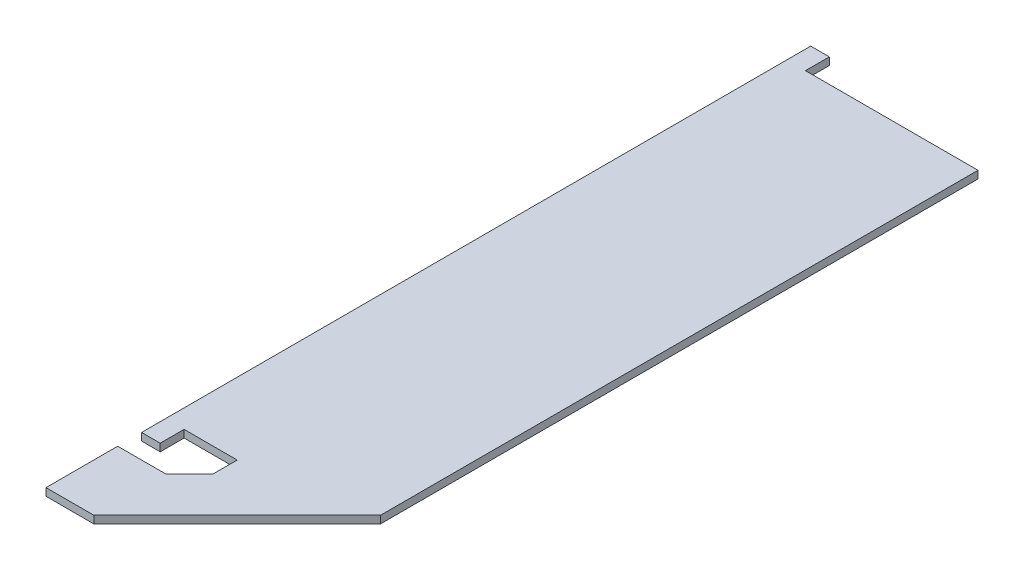
SolidWorks part; units mm, degrees
ref_plane "Front Plane" through (0, 0, 0) normal (0, 0, 1) x (1, 0, 0)
ref_plane "Top Plane" through (0, 0, 0) normal (0, 1, 0) x (1, 0, 0)
ref_plane "Right Plane" through (0, 0, 0) normal (1, 0, 0) x (0, 0, -1)
sketch "Sketch1" plane through (0, 0, 0) normal (0, 1, 0) x (1, 0, 0)
  line L0 (-3.175, -41.275) -> (-3.175, -47.625)
  line L1 (-12.7, -41.275) -> (-3.175, -41.275)
  line L2 (-12.7, -41.275) -> (-12.7, 41.275)
  line L3 (-12.7, 41.275) -> (12.7, 41.275)
  line L4 (12.7, -41.275) -> (12.7, 41.275)
  line L5 (-12.7, -41.275) -> (12.7, 41.275) construction
  line L6 (-12.7, 41.275) -> (12.7, -41.275) construction
  line L7 (-3.175, -47.625) -> (-12.7, -47.625)
  line L8 (-12.7, -47.625) -> (-12.7, -57.15)
  line L9 (-12.7, -57.15) -> (12.7, -57.15)
  line L10 (12.7, -57.15) -> (12.7, -41.275)
  point P0 (0, 0)
  dimension "D1" = 25.4
  dimension "D2" = 82.55
  dimension "D3" = 15.875
  dimension "D4" = 6.35
  dimension "D5" = 15.875
extrude "Boss-Extrude1" add sketch "Sketch1" along normal blind 1.0008
sketch "Sketch2" plane through (0, 0, 41.275) normal (0, 0, 1) x (1, 0, 0)
  line L0 (-12.7, 1.0008) -> (-3.175, 1.0008) construction
  line L1 (-12.7, 0) -> (-10.2279, 0)
  line L2 (-12.7, 0) -> (-12.7, 1.0008)
  line L3 (-12.7, 1.0008) -> (-10.2279, 1.0008)
  line L4 (-10.2279, 0) -> (-10.2279, 1.0008)
  dimension "D1" = 2.667
extrude "Boss-Extrude2" add sketch "Sketch2" along normal blind 3.175
mirror "Mirror1" about plane through (0, 0, 0) normal (0, 0, 1) of "Boss-Extrude2"
chamfer "Chamfer2" distance 19.05 angle 45 1 edges at (12.7, 0.5004, 57.15)
chamfer "Chamfer3" distance 3.175 angle 45 1 edges at (-3.175, 0.5004, 47.625)
equation "\"looseTol\"= 0.02in"
equation "\"tightTol\"= 0.005in"
equation "\"normTol\"= 0.01in"
equation "\"D1@Sketch2\"=0.125000in-\"looseTol\""
